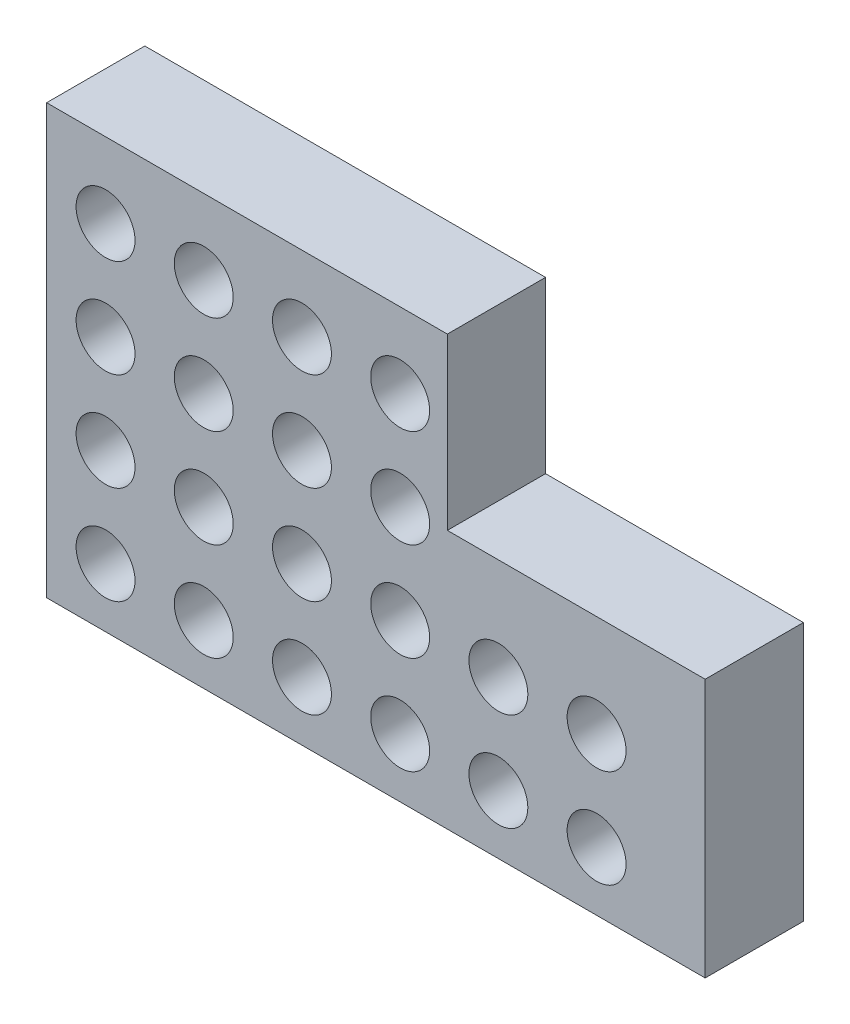
SolidWorks part; units mm, degrees
ref_plane "Front Plane" through (0, 0, 0) normal (0, 0, 1) x (1, 0, 0)
ref_plane "Top Plane" through (0, 0, 0) normal (0, 1, 0) x (1, 0, 0)
ref_plane "Right Plane" through (0, 0, 0) normal (1, 0, 0) x (0, 0, -1)
sketch "Sketch1" plane through (0, 0, 0) normal (0, 0, 1) x (1, 0, 0)
  line L0 (0, 0) -> (0, 43.658)
  line L1 (0, 43.658) -> (40.8045, 43.658)
  line L2 (40.8045, 43.658) -> (40.8045, 26.347)
  line L3 (40.8045, 26.347) -> (67.0564, 26.347)
  line L4 (67.0564, 26.347) -> (67.0564, 4.2802)
  line L5 (67.0564, 4.2802) -> (67.0564, 0)
  line L6 (67.0564, 0) -> (0, 0)
extrude "Boss-Extrude1" add sketch "Sketch1" along normal blind 10
sketch "Sketch2" plane through (0, 0, 10) normal (0, 0, 1) x (1, 0, 0)
  line L0 (0, 43.658) -> (0, 0) construction
  line L2 (0, 0) -> (67.0564, 0) construction
  circle A0 centre (6, 6) radius 3
  point P6 (7.4772, 0)
  dimension "D1" = 6
  dimension "D2" = 6
  dimension "D3" = 6
extrude "Cut-Extrude1" cut sketch "Sketch2" against normal up to surface (10 mm away) up to face at (35.9536, 23.335, 0)
pattern_linear "LPattern1" count 6 spacing 10 along (1, 0, 0) count 4 spacing 10 along (0, 1, 0) skipping (4, 2), (4, 3), (5, 2), (5, 3) of "Cut-Extrude1"
